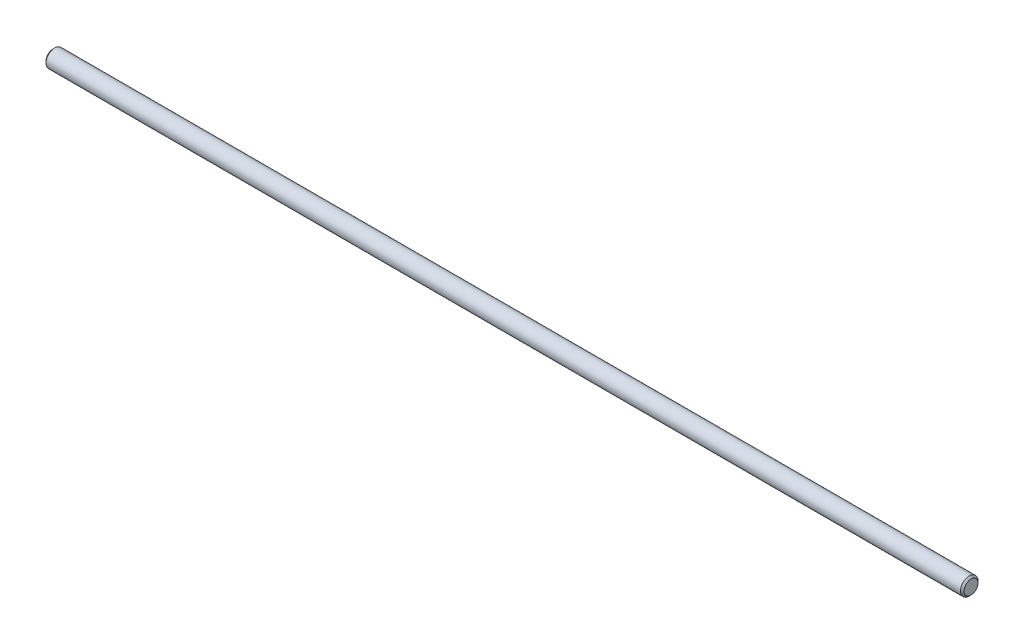
SolidWorks part; units mm, degrees
ref_plane "Front Plane" through (0, 0, 0) normal (0, 0, 1) x (1, 0, 0)
ref_plane "Top Plane" through (0, 0, 0) normal (0, 1, 0) x (1, 0, 0)
ref_plane "Right Plane" through (0, 0, 0) normal (1, 0, 0) x (0, 0, -1)
sketch "Sketch1" plane through (0, 0, 0) normal (1, 0, 0) x (0, 0, -1)
  circle A0 centre (0, 0) radius 4
  dimension "D1" = 8
extrude "Boss-Extrude1" add sketch "Sketch1" along normal mid plane 420
cosmetic thread "Cosmetic Thread5" parameters "D1"=5, "D2"=5.891
cosmetic thread "Cosmetic Thread8" parameters "D1"=10, "D2"=6.891
chamfer "Chamfer1" distance 0.8 angle 45 2 edges at (-210, 0, -4) (210, 0, -4)
